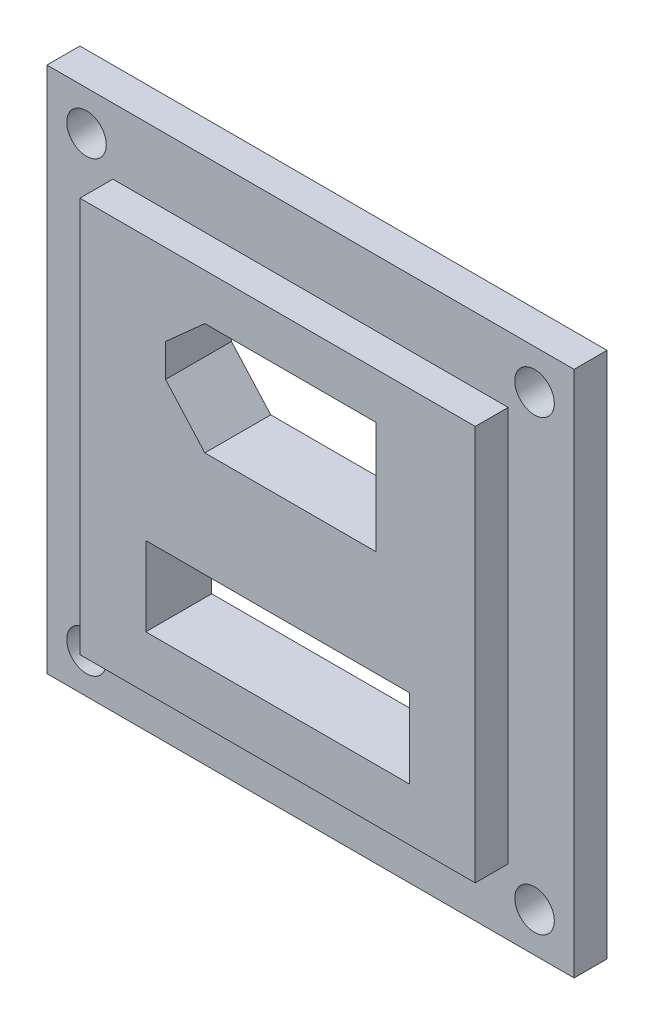
SolidWorks part; units mm, degrees
ref_plane "Front Plane" through (0, 0, 0) normal (0, 0, 1) x (1, 0, 0)
ref_plane "Top Plane" through (0, 0, 0) normal (0, 1, 0) x (1, 0, 0)
ref_plane "Right Plane" through (0, 0, 0) normal (1, 0, 0) x (0, 0, -1)
sketch "Sketch1" plane through (0, 0, 0) normal (0, 0, 1) x (1, 0, 0)
  line L1 (0, 0) -> (40, 0)
  line L2 (0, 0) -> (0, 40)
  line L3 (0, 40) -> (40, 40)
  line L4 (40, 0) -> (40, 40)
  dimension "D1" = 40
  dimension "D2" = 40
extrude "Boss-Extrude2" add sketch "Sketch1" along normal blind 2.5
sketch "Sketch2" plane through (0, 0, 2.5) normal (0, 0, 1) x (1, 0, 0)
  line L0 (40, 40) -> (0, 40) construction
  line L1 (5, 35) -> (35, 35)
  line L2 (5, 35) -> (5, 5)
  line L3 (5, 5) -> (35, 5)
  line L4 (35, 35) -> (35, 5)
  line L5 (40, 0) -> (40, 40) construction
  dimension "D1" = 30
  dimension "D2" = 30
  dimension "D3" = 5
  dimension "D4" = 5
extrude "Boss-Extrude3" add sketch "Sketch2" along normal blind 2.5
sketch "Sketch3" plane through (0, 0, 2.5) normal (0, 0, 1) x (1, 0, 0)
  line L0 (40, 40) -> (0, 40) construction
  line L1 (0, 40) -> (0, 0) construction
  line L2 (40, 0) -> (40, 40) construction
  line L3 (0, 0) -> (40, 0) construction
  circle A0 centre (3, 37) radius 1.5
  circle A1 centre (37, 37) radius 1.5
  circle A2 centre (37, 3) radius 1.5
  circle A3 centre (3, 3) radius 1.5
  point P14 (0, 0)
  point P16 (40.6034, 1.9286)
  dimension "D3" = 3
  dimension "D4" = 3
  dimension "D9" = 3
  dimension "D12" = 3
  dimension "D1" = 3
  dimension "D2" = 3
  dimension "D5" = 3
  dimension "D6" = 3
  dimension "D7" = 3
  dimension "D8" = 3
  dimension "D10" = 3
  dimension "D11" = 3
extrude "Cut-Extrude1" cut sketch "Sketch3" against normal blind 2.5
sketch "Sketch4" plane through (0, 0, 5) normal (0, 0, 1) x (1, 0, 0)
  line L0 (20, 35) -> (20, 5) construction
  line L1 (35, 35) -> (5, 35) construction
  line L2 (5, 5) -> (35, 5) construction
  line L3 (5, 20) -> (35, 20) construction
  line L4 (5, 35) -> (5, 5) construction
  line L5 (35, 5) -> (35, 35) construction
  line L6 (27.4814, 31.5) -> (14.4814, 31.5)
  line L7 (14.4814, 31.5) -> (11.5, 28.8333)
  line L8 (11.5, 28.8333) -> (11.5, 26.3333)
  line L9 (11.5, 26.3333) -> (14.4814, 23)
  line L10 (14.4814, 23) -> (27.4814, 23)
  line L11 (27.4814, 23) -> (27.4814, 31.5)
  line L12 (5, 35) -> (5, 5) construction
  line L13 (10, 15) -> (30, 15)
  line L14 (10, 15) -> (10, 9)
  line L15 (10, 9) -> (30, 9)
  line L16 (30, 15) -> (30, 9)
  dimension "D1" = 13
  dimension "D2" = 13
  dimension "D3" = 8.5
  dimension "D4" = 4
  dimension "D5" = 2.5
  dimension "D6" = 3
  dimension "D7" = 6.5
  dimension "D8" = 20
  dimension "D9" = 6
  dimension "D10" = 5
  dimension "D11" = 5
extrude "Cut-Extrude2" cut sketch "Sketch4" against normal blind 5
